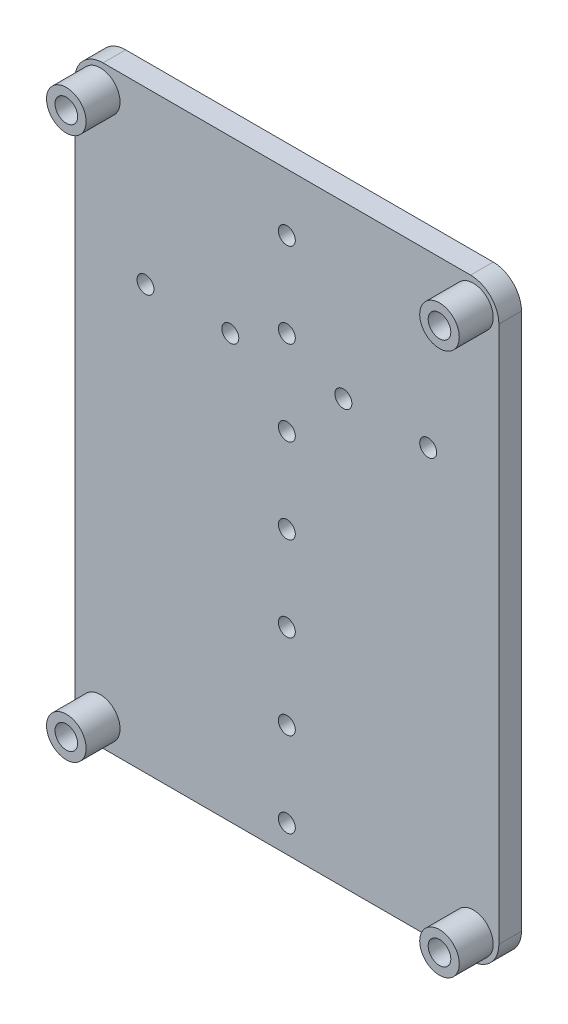
SolidWorks part; units mm, degrees
ref_plane "Front Plane" through (0, 0, 0) normal (0, 0, 1) x (1, 0, 0)
ref_plane "Top Plane" through (0, 0, 0) normal (0, 1, 0) x (1, 0, 0)
ref_plane "Right Plane" through (0, 0, 0) normal (1, 0, 0) x (0, 0, -1)
sketch "Sketch1" plane through (0, 0, 116.6947) normal (0, 0, -1) x (-1, 0, 0)
  line L1 (-172.0266, 164.8119) -> (-97.0266, 164.8119)
  line L2 (-172.0266, 164.8119) -> (-172.0266, 59.8119)
  line L3 (-172.0266, 59.8119) -> (-97.0266, 59.8119)
  line L4 (-97.0266, 164.8119) -> (-97.0266, 59.8119)
  circle A0 centre (-134.5266, 154.6371) radius 1.5
  circle A1 centre (-134.5266, 139.6371) radius 1.5
  circle A2 centre (-144.5266, 134.6371) radius 1.5
  circle A3 centre (-159.5266, 134.6371) radius 1.5
  circle A4 centre (-124.5266, 134.6371) radius 1.5
  circle A5 centre (-109.5266, 134.6371) radius 1.5
  circle A6 centre (-134.5266, 124.6371) radius 1.5
  circle A7 centre (-134.5266, 109.6371) radius 1.5
  circle A8 centre (-134.5266, 94.6371) radius 1.5
  circle A9 centre (-134.5266, 79.6371) radius 1.5
  circle A10 centre (-134.5266, 64.6371) radius 1.5
  circle A11 centre (-167.5266, 64.3119) radius 2
  circle A12 centre (-101.5266, 64.3119) radius 2
  circle A13 centre (-101.5266, 160.3119) radius 2
  circle A14 centre (-167.5266, 160.3119) radius 2
extrude "Boss-Extrude1" add sketch "Sketch1" along normal blind 4
sketch "Sketch2" plane through (0, 0, 116.6947) normal (0, 0, 1) x (1, 0, 0)
  circle A0 centre (101.5266, 160.3119) radius 2
  circle A1 centre (101.5266, 160.3119) radius 3.5
  circle A2 centre (167.5266, 160.3119) radius 2
  circle A3 centre (167.5266, 160.3119) radius 3.5
  circle A4 centre (101.5266, 64.3119) radius 2
  circle A5 centre (101.5266, 64.3119) radius 3.5
  circle A6 centre (167.5266, 64.3119) radius 2
  circle A7 centre (167.5266, 64.3119) radius 3.5
  dimension "D1" = 7
  dimension "D2" = 7
  dimension "D3" = 7
  dimension "D4" = 7
extrude "Boss-Extrude2" add sketch "Sketch2" along normal blind 6
fillet "Fillet1" radius 5 4 edges at (97.0266, 59.8119, 114.6947) (172.0266, 59.8119, 114.6947) (172.0266, 164.8119, 114.6947) (97.0266, 164.8119, 114.6947)
